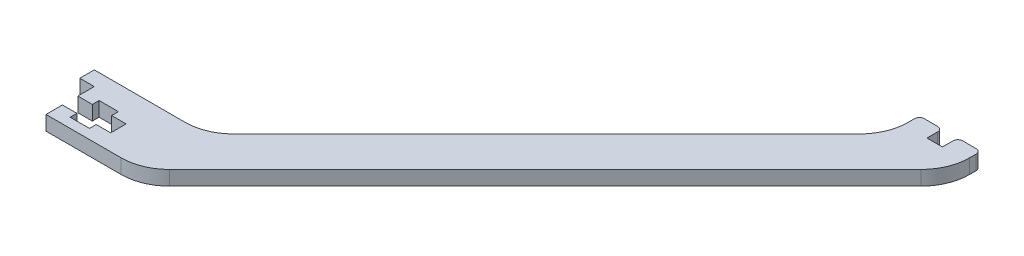
SolidWorks part; units mm, degrees
ref_plane "Alzado" through (0, 0, 0) normal (0, 0, 1) x (1, 0, 0)
ref_plane "Planta" through (0, 0, 0) normal (0, 1, 0) x (1, 0, 0)
ref_plane "Vista lateral" through (0, 0, 0) normal (1, 0, 0) x (0, 0, -1)
sketch "Croquis1" plane through (0, 0, 0) normal (0, 1, 0) x (1, 0, 0)
  line L0 (7, 3.4) -> (7, 2)
  line L2 (0, 0) -> (15.5858, 0)
  line L3 (0, 0) -> (0, 10)
  line L4 (-3, 13) -> (15.8579, 13)
  line L7 (0, 10) -> (-3, 10)
  line L8 (-3, 13) -> (-3, 10)
  line L9 (7, 6.6) -> (10, 6.6)
  line L10 (0, 6.6) -> (3, 6.6)
  line L11 (0, 6.6) -> (0, 3.4)
  line L12 (0, 3.4) -> (3, 3.4)
  line L13 (10, 6.6) -> (10, 3.4)
  line L14 (3, 3.4) -> (3, 2)
  line L15 (3, 8) -> (7, 8)
  line L16 (3, 8) -> (3, 6.6)
  line L17 (3, 2) -> (7, 2)
  line L18 (7, 8) -> (7, 6.6)
  line L19 (7, 3.4) -> (10, 3.4)
  line L21 (22.9289, 15.9289) -> (87.7817, 80.7817)
  line L22 (20, 0) -> (20, 0.2721)
  line L23 (22.6569, 2.9289) -> (100.5097, 80.7817)
  line L24 (90.7107, 87.8528) -> (90.7107, 90.2107)
  line L29 (90.7107, 90.2107) -> (95.4736, 90.2107)
  line L30 (103.4386, 90.2107) -> (103.4386, 87.8528)
  line L31 (98.6736, 90.2107) -> (103.4386, 90.2107)
  line L33 (95.4736, 90.2107) -> (95.4736, 87.0107)
  line L34 (95.4736, 87.0107) -> (98.6736, 87.0107)
  line L35 (98.6736, 90.2107) -> (98.6736, 87.0107)
  arc A0 (22.6569, 2.9289) -> (15.5858, 0) centre (15.5858, 10) cw
  arc A1 (103.4386, 87.8528) -> (100.5097, 80.7817) centre (93.4386, 87.8528) cw
  arc A2 (87.7817, 80.7817) -> (90.7107, 87.8528) centre (80.7107, 87.8528) ccw
  arc A3 (15.8579, 13) -> (22.9289, 15.9289) centre (15.8579, 23) ccw
  point P21 (3, 7.3)
  point P23 (79.0675, 59.5254)
  point P26 (-3, 10.0244)
  point P28 (87.1321, 67.4042)
  point P31 (75.0908, 68.0908)
  point P33 (75.9151, 68.9151)
  point P34 (77.8226, 70.8226)
  point P35 (99.8566, 87.6403)
  point P36 (105.8103, 93.3584)
  point P37 (102.1067, 90.1581)
  point P38 (107.6812, 94.0618)
  point P39 (99.7162, 94.4725)
  point P40 (0, 0)
  point P41 (0, 0)
  point P47 (103.4386, 83.7107)
  point P50 (90.7107, 83.7107)
  point P53 (20, 13)
  dimension "D3" = 10
  dimension "D2" = 3
  dimension "D4" = 3.2
  dimension "D5" = 10
  dimension "D6" = 4
  dimension "D7" = 6
  dimension "D8" = 1.4
  dimension "D9" = 13
  dimension "D10" = 2
  dimension "D11" = 3
  dimension "D12" = 135
  dimension "D13" = 3
  dimension "D14" = 23
  dimension "D15" = 9
  dimension "D16" = 3.2
  dimension "D17" = 4.765
  dimension "D18" = 3.2
  dimension "D19" = 100
  dimension "D20" = 6.5
extrude "Saliente-Extruir1" add sketch "Croquis1" along normal blind 3 contours L31 L35 L34 L33 L29 L24 L21 L4 L8 L7 L3 L10 L16 L15 L18 L9 L13 L19 L0 L17 L14 L12 L2 L22 L23 L30
fillet "Redondeo1" radius 1 4 edges at (95.4736, 1.5, -90.2107) (98.6736, 1.5, -90.2107) (103.4386, 1.5, -90.2107) (90.7107, 1.5, -90.2107)
